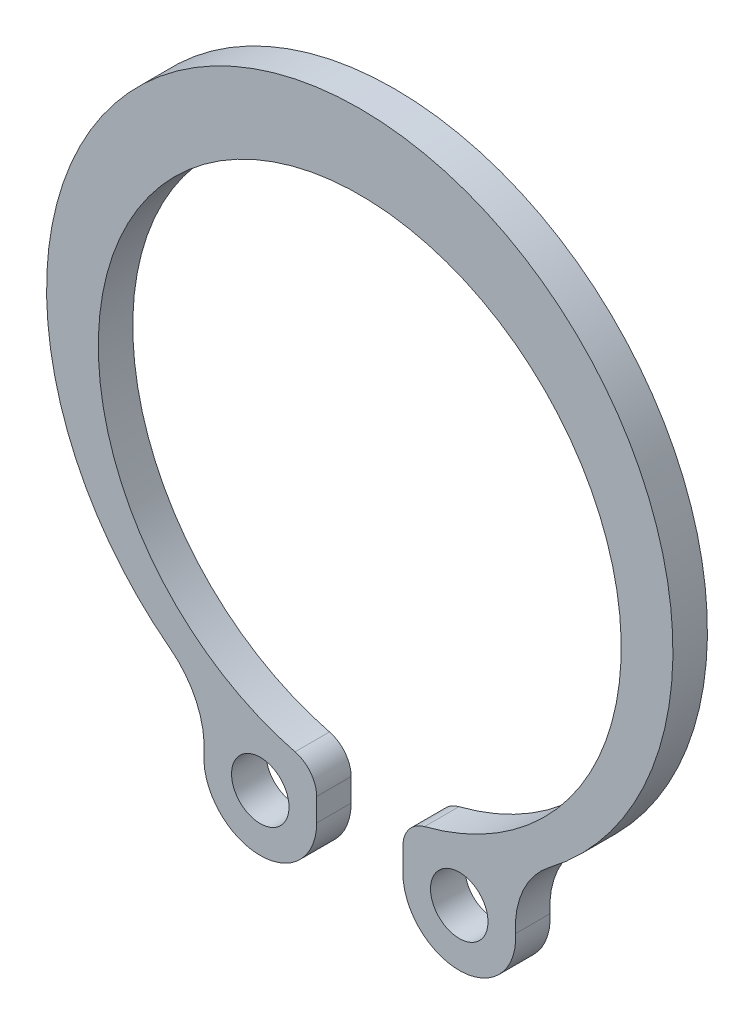
SolidWorks part; units mm, degrees
material "AISI Тип A2 Инструментальная сталь"
ref_plane "Спереди" through (0, 0, 0) normal (0, 0, 1) x (1, 0, 0)
ref_plane "Сверху" through (0, 0, 0) normal (0, 1, 0) x (1, 0, 0)
ref_plane "Справа" through (0, 0, 0) normal (1, 0, 0) x (0, 0, -1)
sketch "Эскиз1" plane through (0, 0, 0) normal (0, 0, 1) x (1, 0, 0)
  line L0 (0, -1000) -> (0, 49000) construction
  line L1 (-1.5, -11.385) -> (-1.5, -10.5857)
  line L2 (1.5, -11.385) -> (1.5, -10.5857)
  arc A0 (6.5992, -8.6753) -> (-6.5992, -8.6753) centre (0, 0) ccw
  arc A1 (2.2525, -9.6168) -> (-2.2525, -9.6168) centre (0, -0.8) ccw
  circle A2 centre (-3.4629, -11.385) radius 1
  arc A3 (-5.4218, -11.2576) -> (-1.5, -11.385) centre (-3.4629, -11.385) ccw
  arc A4 (-2.2525, -9.6168) -> (-1.5, -10.5857) centre (-2.5, -10.5857) cw
  arc A5 (-6.5992, -8.6753) -> (-5.4218, -11.2576) centre (-8.4154, -11.063) cw
  arc A6 (6.5992, -8.6753) -> (5.4218, -11.2576) centre (8.4154, -11.063) ccw
  arc A7 (2.2525, -9.6168) -> (1.5, -10.5857) centre (2.5, -10.5857) ccw
  arc A8 (5.4218, -11.2576) -> (1.5, -11.385) centre (3.4629, -11.385) cw
  circle A9 centre (3.4629, -11.385) radius 1
  point P12 (-64.8352, 6.3383)
  point P17 (-1.5, -9.7755)
  dimension "D2" = 18.2
  dimension "D3" = 21.8
  dimension "D4" = 2
  dimension "r1" = 3
  dimension "r2" = 1
  dimension "e" = 0.8
  dimension "l" = 3
  dimension "a" = 4
extrude "Бобышка-Вытянуть1" add sketch "Эскиз1" along normal blind 1.2
